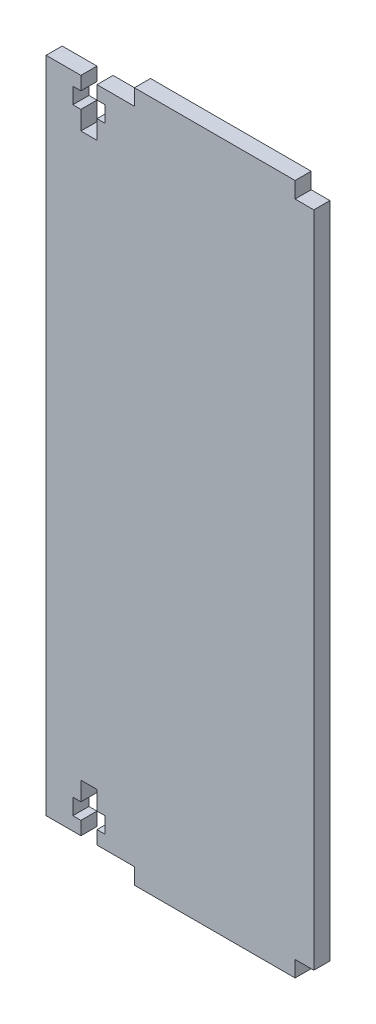
SolidWorks part; units mm, degrees
ref_plane "Front Plane" through (0, 0, 0) normal (0, 0, 1) x (1, 0, 0)
ref_plane "Top Plane" through (0, 0, 0) normal (0, 1, 0) x (1, 0, 0)
ref_plane "Right Plane" through (0, 0, 0) normal (1, 0, 0) x (0, 0, -1)
sketch "Sketch1" plane through (0, 0, 0) normal (0, 0, 1) x (1, 0, 0)
  line L0 (-15.5, 61.5) -> (-8.5, 61.5)
  line L1 (-25, 61.5) -> (-18.5, 61.5)
  line L2 (-25, 61.5) -> (-25, -61.5)
  line L3 (-25, -61.5) -> (-18.5, -61.5)
  line L4 (25, 61.5) -> (25, -61.5)
  line L5 (-15.5, 59) -> (-14, 59)
  line L7 (-8.5, 64.5) -> (21.5, 64.5)
  line L8 (-8.5, 64.5) -> (-8.5, 61.5)
  line L9 (-8.5, -64.5) -> (21.5, -64.5)
  line L10 (21.5, 64.5) -> (21.5, 61.5)
  line L13 (-18.5, -52.5) -> (-15.5, -52.5)
  line L14 (-18.5, -52.5) -> (-18.5, -56)
  line L16 (-15.5, -52.5) -> (-15.5, -56)
  line L17 (-8.5, -61.5) -> (-8.5, -64.5)
  line L18 (21.5, -61.5) -> (25, -61.5)
  line L19 (-20, -59) -> (-18.5, -59)
  line L20 (-20, -59) -> (-20, -56)
  line L21 (-20, -56) -> (-18.5, -56)
  line L22 (-14, -59) -> (-14, -56)
  line L23 (21.5, -61.5) -> (21.5, -64.5)
  line L24 (-18.5, 59) -> (-18.5, 61.5)
  line L25 (21.5, 61.5) -> (25, 61.5)
  line L29 (-14, 59) -> (-14, 56)
  line L30 (-20, 56) -> (-18.5, 56)
  line L31 (-20, 59) -> (-20, 56)
  line L32 (-20, 59) -> (-18.5, 59)
  line L33 (-15.5, 52.5) -> (-15.5, 56)
  line L34 (-18.5, 52.5) -> (-18.5, 56)
  line L35 (-18.5, 52.5) -> (-15.5, 52.5)
  line L36 (-15.5, -61.5) -> (-8.5, -61.5)
  line L37 (-15.5, -59) -> (-14, -59)
  line L38 (-18.5, -59) -> (-18.5, -61.5)
  line L41 (-15.5, -59) -> (-15.5, -61.5)
  line L42 (-15.5, 56) -> (-14, 56)
  line L43 (-15.5, 59) -> (-15.5, 61.5)
  line L45 (-15.5, -56) -> (-14, -56)
  point P0 (0, 0)
  point P6 (5, 0)
  point P11 (-17, -57.5)
  point P12 (-17, -57)
  point P31 (-17, 57)
  point P32 (-17, 57.5)
  dimension "D1" = 123
  dimension "D2" = 50
extrude "Boss-Extrude1" add sketch "Sketch1" along normal blind 3
